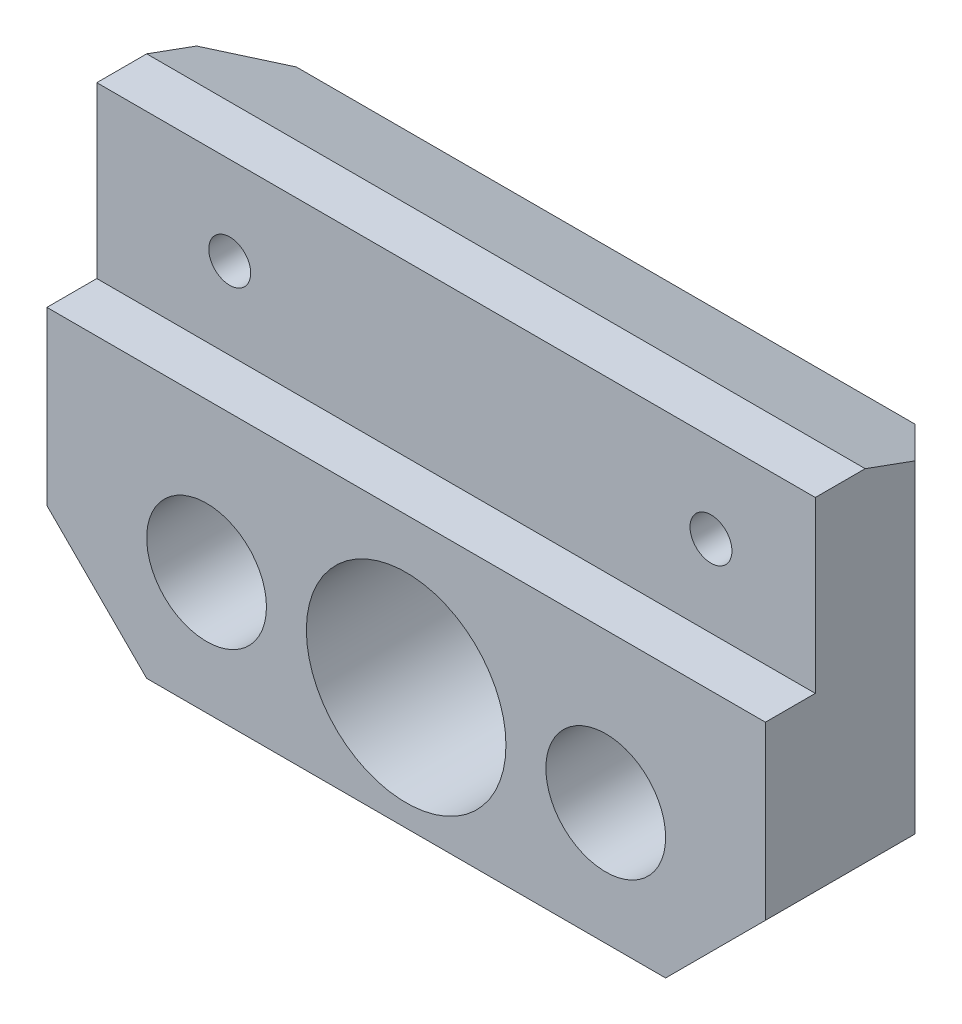
SolidWorks part; units mm, degrees
ref_plane "Ebene vorne" through (0, 0, 0) normal (0, 0, 1) x (1, 0, 0)
ref_plane "Ebene oben" through (0, 0, 0) normal (0, 1, 0) x (1, 0, 0)
ref_plane "Ebene rechts" through (0, 0, 0) normal (1, 0, 0) x (0, 0, -1)
sketch "Skizze1" plane through (0, 0, 0) normal (0, 0, 1) x (1, 0, 0)
  line L0 (0, 0) -> (107.9023, 0) construction
  line L1 (53.9613, 30.0276) -> (53.9613, -49.8276) construction
  line L3 (17.9613, 22.1) -> (89.9613, 22.1)
  line L4 (17.9613, 22.1) -> (17.9613, -22.1)
  line L5 (17.9613, -22.1) -> (89.9613, -22.1)
  line L6 (89.9613, 22.1) -> (89.9613, -22.1)
  circle A0 centre (53.9613, -9.9) radius 10
  circle A1 centre (33.9613, -9.9) radius 6
  circle A2 centre (73.9613, -9.9) radius 6
  dimension "D3" = 20
  dimension "D5" = 40
  dimension "D6" = 12
  dimension "D1" = 44.2
  dimension "D2" = 72
  dimension "D4" = 12.2
extrude "Aufsatz-Linear austragen1" add sketch "Skizze1" along normal blind 20
chamfer "Fase1" distance 10 angle 45 1 edges at (17.9613, -22.1, 10)
chamfer "Fase2" distance 10 angle 45 1 edges at (89.9613, -22.1, 10)
chamfer "Fase6" distance 10 angle 20 1 edges at (53.9613, 22.1, 0)
chamfer "Fase7" distance 5 angle 45 2 edges at (17.9613, 3.1801, 0) (89.9613, 3.1801, 0)
sketch "Skizze3" plane through (17.9613, 0, 0) normal (-1, 0, 0) x (0, 0, 1)
  line L0 (20, 22.1) -> (15, 22.1)
  line L1 (20, 22.1) -> (10, 22.1) construction
  line L2 (20, 22.1) -> (20, -12.1) construction
  line L3 (15, 22.1) -> (15, 5.1)
  line L4 (15, 5.1) -> (20, 5.1)
  line L5 (20, 5.1) -> (20, 22.1)
  dimension "D1" = 17
  dimension "D2" = 5
extrude "Schnitt-Linear austragen1" cut sketch "Skizze3" against normal blind 80
sketch "Skizze11" plane through (0, 0, 0) normal (0, 0, -1) x (-1, 0, 0)
  circle A0 centre (-53.9613, -9.9) radius 12
  dimension "D1" = 24
extrude "Schnitt-Linear austragen2" cut sketch "Skizze11" against normal blind 3.4 contours A0
sketch "Skizze12" plane through (0, 0, 15) normal (0, 0, 1) x (1, 0, 0)
sketch "Skizze13" plane through (0, 0, 15) normal (0, 0, 1) x (1, 0, 0)
  line L0 (17.9613, 22.1) -> (17.9613, 5.1) construction
  line L1 (89.9613, 22.1) -> (89.9613, 5.1) construction
  line L2 (53.9613, -28.9445) -> (53.9613, 31.7738) construction
  circle A0 centre (29.9613, 17.1813) radius 2.5
  circle A1 centre (77.9613, 17.1813) radius 2.5
  dimension "D1" = 5
  dimension "D2" = 48
hole_wizard "M5 Gewindebohrung1" positions "Skizze16" profile "Skizze17" tap size "M5" standard "DIN"
sketch "Skizze16" plane through (0, 0, 15) normal (0, 0, 1) x (1, 0, 0)
  point P0 (31.2827, 13.2732)
  point P2 (79.5056, 13.2732)
cosmetic thread "Gewindedarstellung1" parameters "D2"=5
cosmetic thread "Gewindedarstellung2" parameters "D2"=5
sketch "Skizze17" plane through (31.2827, 13.2732, 15) normal (1, 0, 0) x (0, -1, 0)
  line L0 (0, 0) -> (0, 13.2618)
  line L1 (0, 13.2618) -> (2.1, 12)
  line L2 (2.1, 12) -> (2.1, 0)
  line L5 (2.1, 0) -> (0, 0)
  line L10 (0, 13.2618) -> (-2.1, 12) construction
  line L11 (0, -6.35) -> (0, 107.95) construction
  dimension "Bohrerdurchmesser" = 4.2
  dimension "Bohrungstiefe" = 12
  dimension "Spitzenwinkel" = 118
